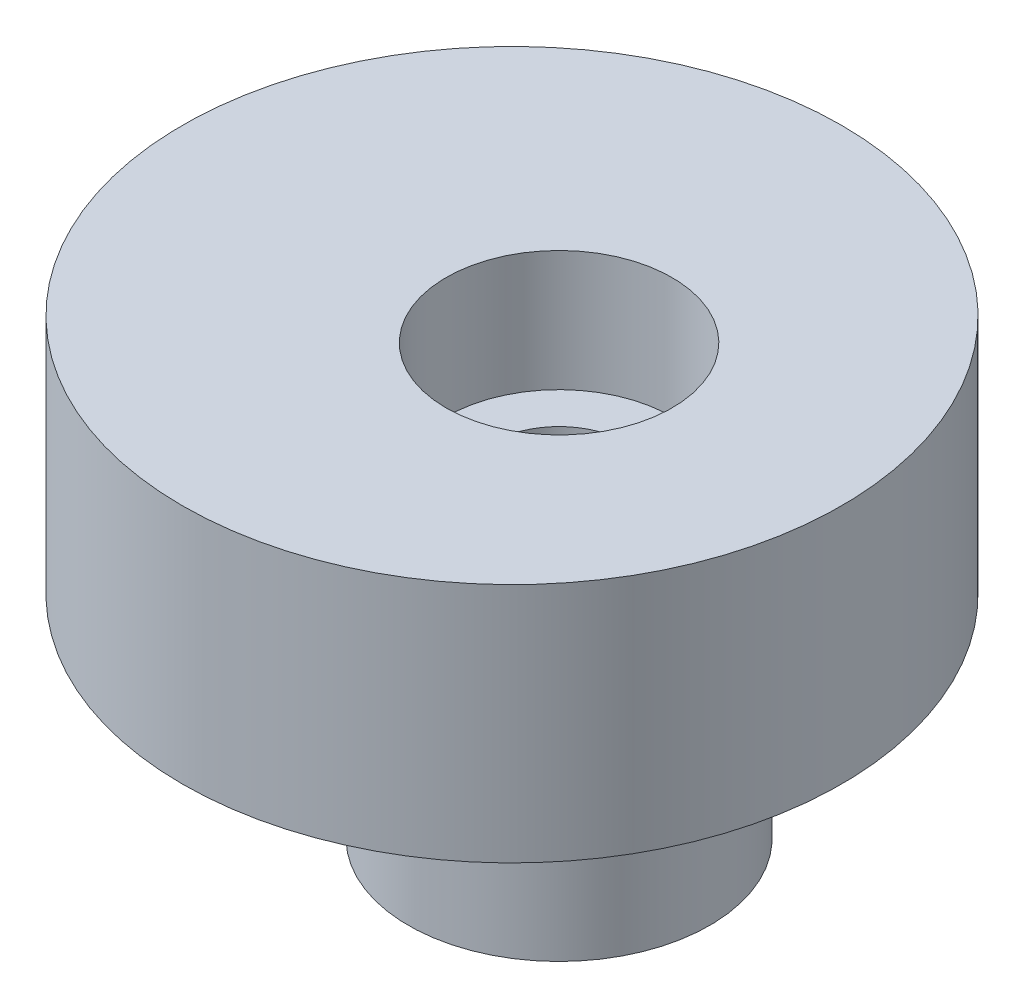
SolidWorks part; units mm, degrees
ref_plane "Спереди" through (0, 0, 0) normal (0, 0, 1) x (1, 0, 0)
ref_plane "Сверху" through (0, 0, 0) normal (0, 1, 0) x (1, 0, 0)
ref_plane "Справа" through (0, 0, 0) normal (1, 0, 0) x (0, 0, -1)
sketch "Эскиз1" plane through (0, 0, 0) normal (0, 1, 0) x (1, 0, 0)
  line L0 (-10, 0) -> (11.7383, 0) construction
  circle A0 centre (0, 0) radius 1.8
  circle A1 centre (0, 0) radius 10 construction
  circle A2 centre (-1.25, 0) radius 8.75
  point P4 (7.5, 0)
  point P5 (10, 0)
  point P6 (-10, 0)
  dimension "D1" = 3.6
  dimension "D2" = 20
  dimension "D3" = 2.5
extrude "Бобышка-Вытянуть1" add sketch "Эскиз1" along normal blind 6.4
sketch "Эскиз7" plane through (0, 6.4, 0) normal (0, 1, 0) x (1, 0, 0)
  circle A0 centre (0, 0) radius 3
  dimension "D1" = 6
extrude "Вырез-Вытянуть1" cut sketch "Эскиз7" against normal blind 3.2
sketch "Эскиз8" plane through (0, 0, 0) normal (0, -1, 0) x (1, 0, 0)
  circle A0 centre (0, 0) radius 1.8
  circle A1 centre (0, 0) radius 4
  dimension "D1" = 8
extrude "Бобышка-Вытянуть2" add sketch "Эскиз8" along normal blind 5
sketch "Эскиз9" plane through (0, 0, 0) normal (0, -1, 0) x (1, 0, 0)
  circle A0 centre (0, 0) radius 4
  circle A1 centre (0, 0) radius 5.65
  dimension "D1" = 11.3
extrude "Вырез-Вытянуть2" cut sketch "Эскиз9" against normal blind 2
